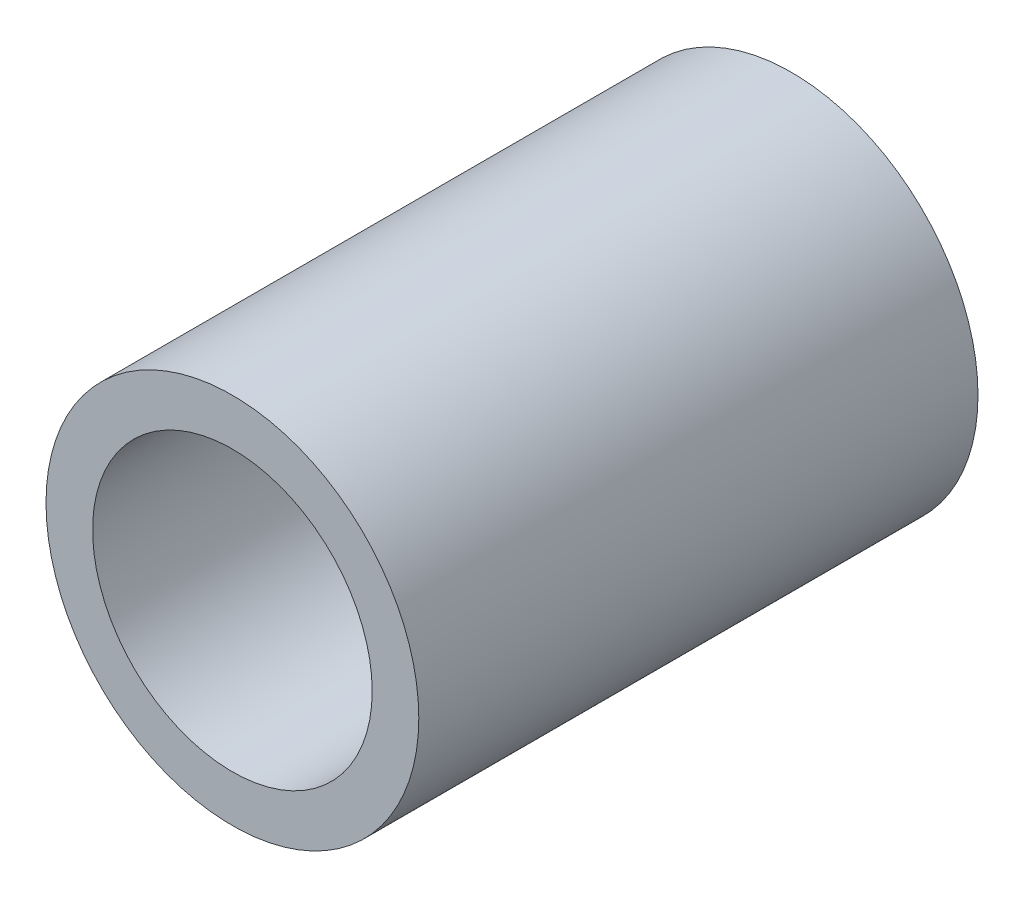
SolidWorks part; units mm, degrees
ref_plane "Front Plane" through (0, 0, 0) normal (0, 0, 1) x (1, 0, 0)
ref_plane "Top Plane" through (0, 0, 0) normal (0, 1, 0) x (1, 0, 0)
ref_plane "Right Plane" through (0, 0, 0) normal (1, 0, 0) x (0, 0, -1)
sketch "Sketch1" plane through (0, 0, 0) normal (0, 0, 1) x (1, 0, 0)
  circle A0 centre (0, 0) radius 25.4
  circle A1 centre (0, 0) radius 19.05
  dimension "D1" = 50.8
  dimension "D2" = 6.35
extrude "Boss-Extrude1" add sketch "Sketch1" along normal blind 76.2
